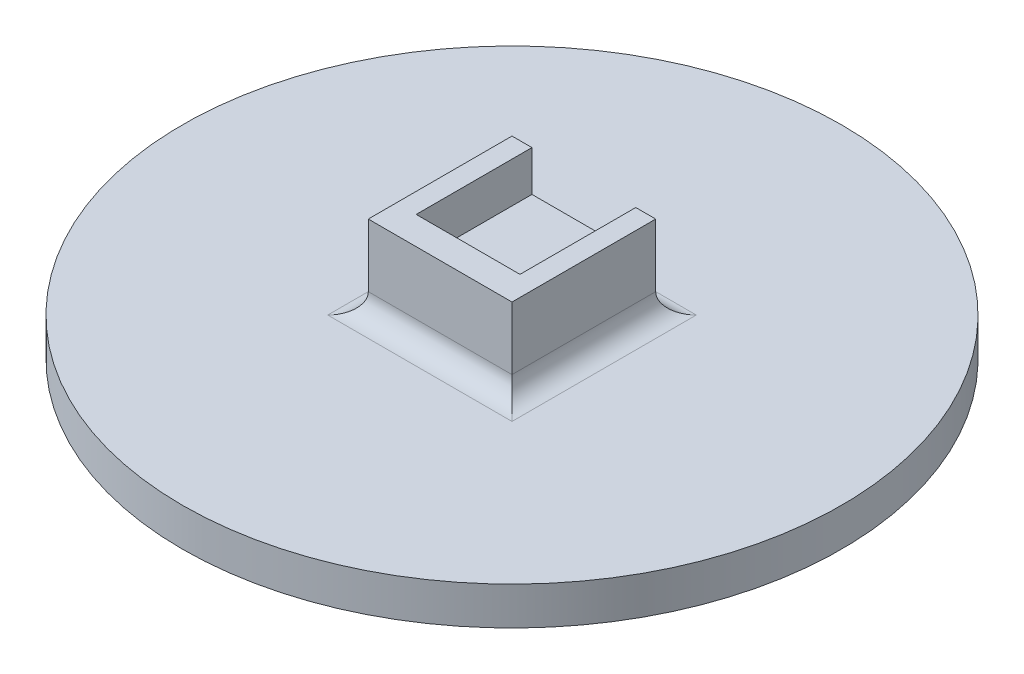
SolidWorks part; units mm, degrees
ref_plane "Front Plane" through (0, 0, 0) normal (0, 0, 1) x (1, 0, 0)
ref_plane "Top Plane" through (0, 0, 0) normal (0, 1, 0) x (1, 0, 0)
ref_plane "Right Plane" through (0, 0, 0) normal (1, 0, 0) x (0, 0, -1)
sketch "Sketch1" plane through (0, 0, 0) normal (0, 1, 0) x (1, 0, 0)
  circle A0 centre (0, 0) radius 41.275
  dimension "D1" = 82.55
extrude "Boss-Extrude1" add sketch "Sketch1" along normal blind 4.7625
sketch "Sketch2" plane through (0, 4.7625, 0) normal (0, 1, 0) x (1, 0, 0)
  line L1 (-9, -9) -> (9, -9)
  line L2 (-9, -9) -> (-9, 9)
  line L3 (-9, 9) -> (9, 9)
  line L4 (9, -9) -> (9, 9)
  line L5 (-9, -9) -> (9, 9) construction
  line L6 (-9, 9) -> (9, -9) construction
  point P0 (0, 0)
  dimension "D1" = 18
  dimension "D2" = 18
extrude "Boss-Extrude2" add sketch "Sketch2" along normal blind 5.334
fillet "Fillet1" radius 2.54 4 edges at (9, 4.7625, 0) (0, 4.7625, -9) (-9, 4.7625, 0) (0, 4.7625, 9)
sketch "Sketch3" plane through (0, 10.0965, 0) normal (0, 1, 0) x (1, 0, 0)
  line L0 (-9, -9) -> (9, -9)
  line L1 (9, -9) -> (9, 9)
  line L2 (-9, -9) -> (-9, 9)
  line L3 (-9, 9) -> (-6.5, 9)
  line L4 (9, 9) -> (-9, 9) construction
  line L5 (-6.5, 9) -> (-6.5, -5.5)
  line L6 (-6.5, -5.5) -> (6.5, -5.5)
  line L7 (6.5, -5.5) -> (6.5, 9)
  line L8 (9, 9) -> (-9, 9) construction
  line L9 (6.5, 9) -> (9, 9)
  dimension "D1" = 2.5
  dimension "D2" = 3.5
  dimension "D3" = 2.5
extrude "Boss-Extrude3" add sketch "Sketch3" along normal blind 5.08
